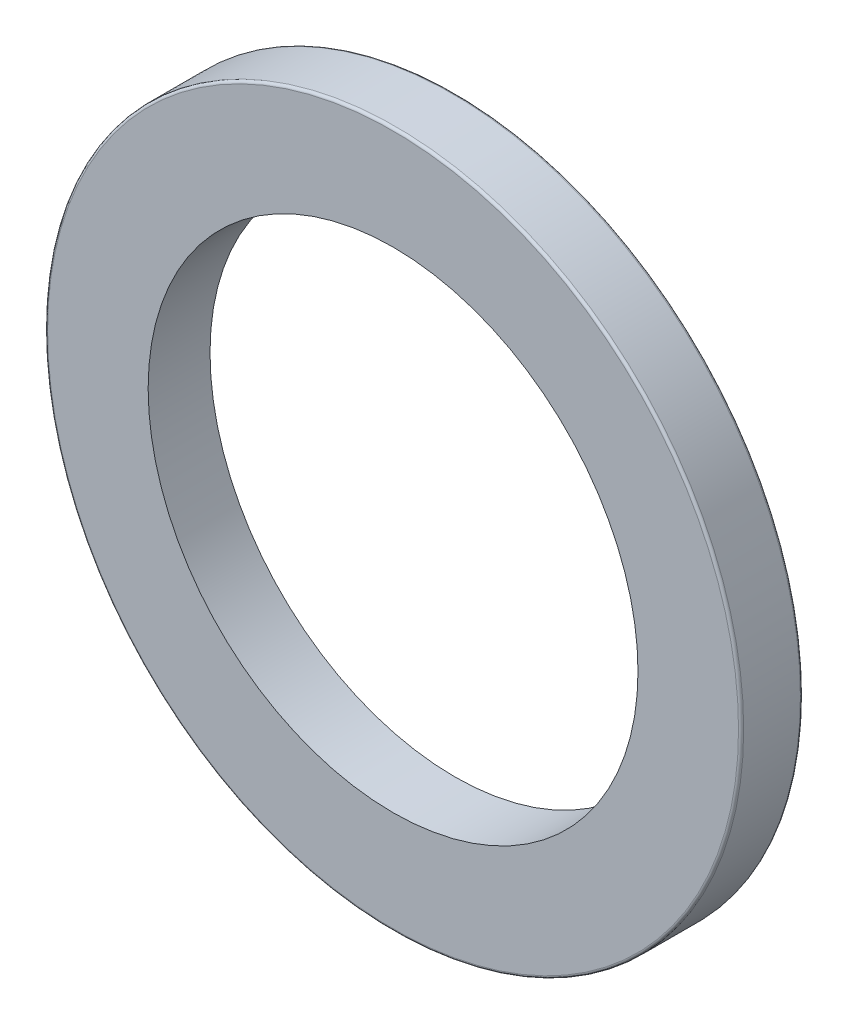
SolidWorks part; units mm, degrees
ref_plane "Front Plane" through (0, 0, 0) normal (0, 0, 1) x (1, 0, 0)
ref_plane "Top Plane" through (0, 0, 0) normal (0, 1, 0) x (1, 0, 0)
ref_plane "Right Plane" through (0, 0, 0) normal (1, 0, 0) x (0, 0, -1)
sketch "Esquisse1" plane through (0, 0, 0) normal (0, 0, 1) x (1, 0, 0)
  circle A0 centre (0, 0) radius 47.5
  circle A1 centre (0, 0) radius 67.5
  dimension "D1" = 135
  dimension "D2" = 95
extrude "Boss.-Extru.1" add sketch "Esquisse1" along normal blind 12
fillet "Congé1" radius 0.5 2 edges at (67.5, 0, 0) (67.5, 0, 12)
